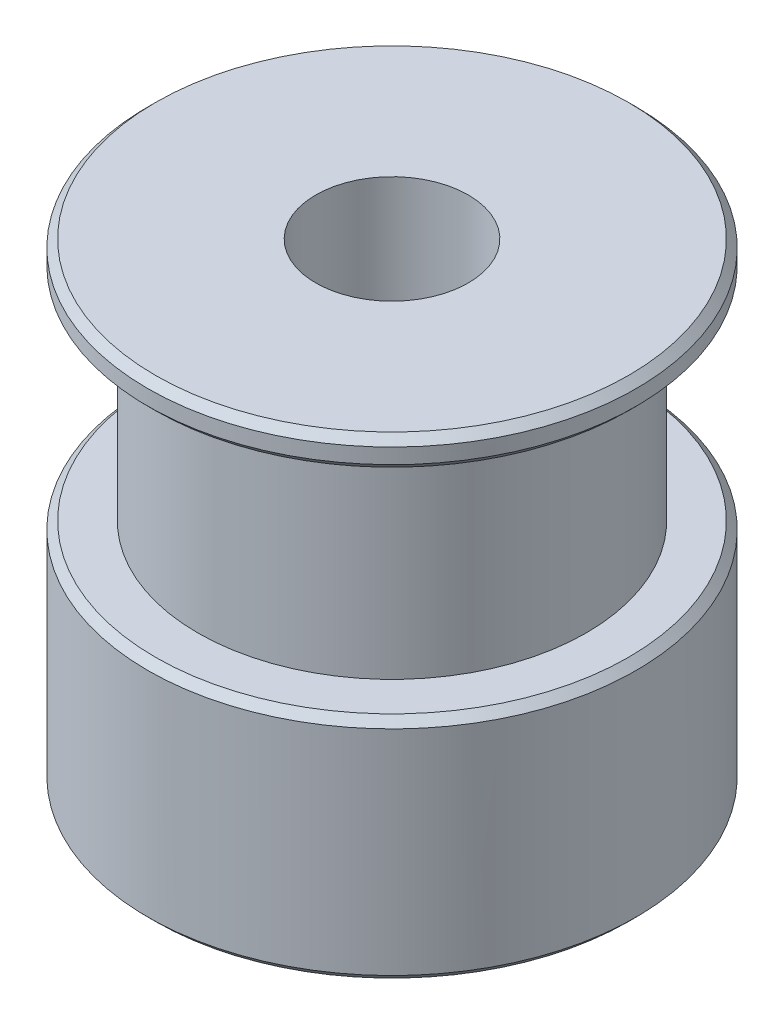
SolidWorks part; units mm, degrees
ref_plane "Front Plane" through (0, 0, 0) normal (0, 0, 1) x (1, 0, 0)
ref_plane "Top Plane" through (0, 0, 0) normal (0, 1, 0) x (1, 0, 0)
ref_plane "Right Plane" through (0, 0, 0) normal (1, 0, 0) x (0, 0, -1)
sketch "Sketch4" plane through (0, 0, 0) normal (0, 0, 1) x (1, 0, 0)
  line L0 (0, 0) -> (0, 15.5) construction
  line L1 (2.5, 0) -> (8, 0)
  line L2 (8, 0) -> (8, 7.5)
  line L3 (8, 7.5) -> (6.3662, 7.5)
  line L4 (6.3662, 7.5) -> (6.3662, 14.5)
  line L5 (6.3662, 14.5) -> (8, 14.5)
  line L6 (8, 14.5) -> (8, 15.5)
  line L7 (8, 15.5) -> (2.5, 15.5)
  line L8 (2.5, 15.5) -> (2.5, 0)
  dimension "D1" = 5
  dimension "D2" = 12.7324
  dimension "D3" = 7
  dimension "D4" = 15.5
  dimension "D5" = 16
  dimension "D6" = 1
revolve "Revolve2" add sketch "Sketch4" angle 360 about L0
chamfer "Chamfer1" distance 0.25 angle 45 4 edges at (0, 0, -8) (0, 7.5, -8) (0, 14.5, -8) (0, 15.5, -8)
equation "\"D2@Sketch4\"   = 40/pi"
